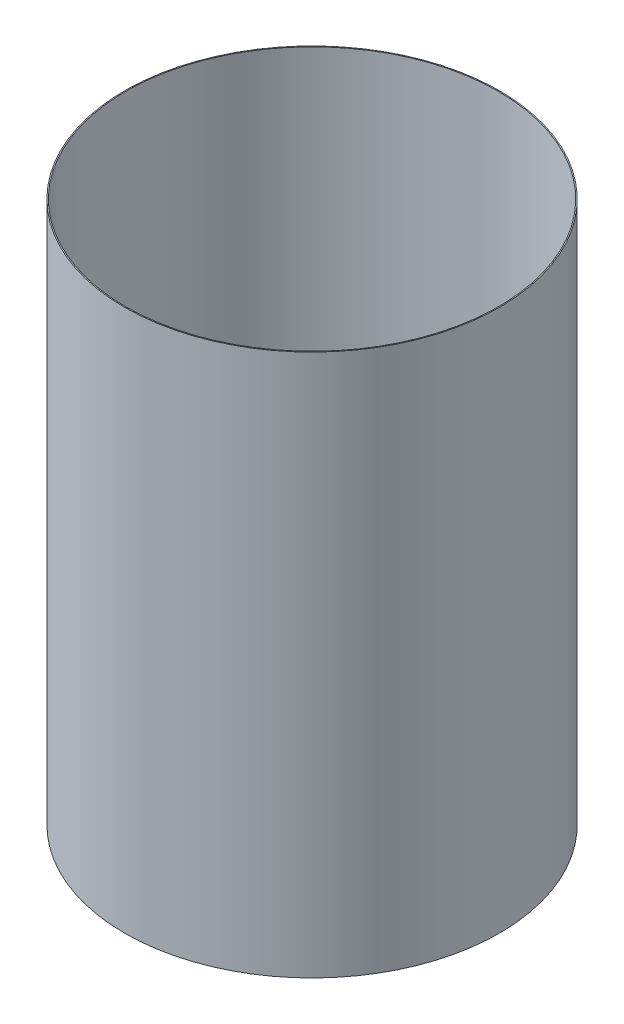
SolidWorks part; units mm, degrees
material "Thornel Mat VMA"
ref_plane "Front Plane" through (0, 0, 0) normal (0, 0, 1) x (1, 0, 0)
ref_plane "Top Plane" through (0, 0, 0) normal (0, 1, 0) x (1, 0, 0)
ref_plane "Right Plane" through (0, 0, 0) normal (1, 0, 0) x (0, 0, -1)
ref_axis "Axis1" through (0, 55, 0) along (0, -1, 0)
sketch "Sketch1" plane through (0, 0, 0) normal (0, 0, 1) x (1, 0, 0)
  line L0 (-45.8724, -19.9059) -> (-45.8724, -153.2559)
  line L2 (-38.1, -19.9059) -> (0, -19.9059) construction
  line L3 (-38.1, -153.2559) -> (0, -153.2559) construction
revolve "Revolve-Thin1" add sketch "Sketch1" angle 360 about axis through (0, 55, 0) along (0, -1, 0)
equation "\"D3@Revolve-Thin1\"=\"CF THICKNESS@Cryo Tank.Assembly\""
